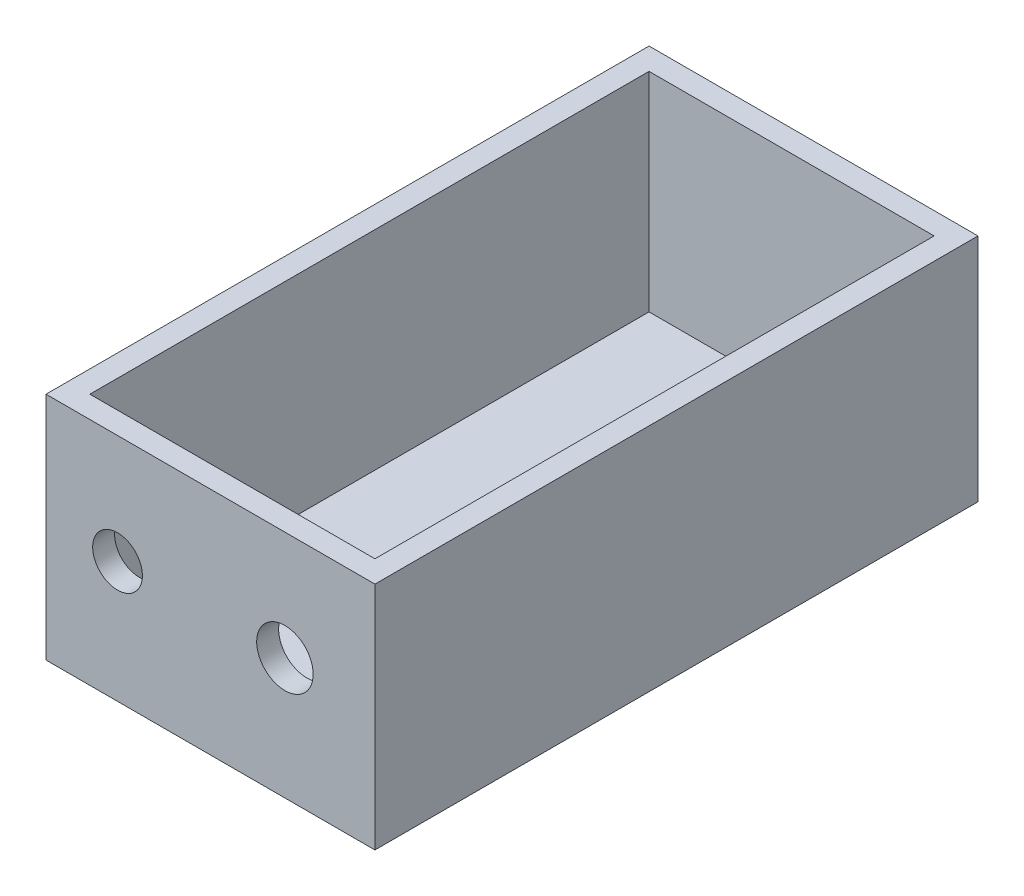
SolidWorks part; units mm, degrees
ref_plane "Спереди" through (0, 0, 0) normal (0, 0, 1) x (1, 0, 0)
ref_plane "Сверху" through (0, 0, 0) normal (0, 1, 0) x (1, 0, 0)
ref_plane "Справа" through (0, 0, 0) normal (1, 0, 0) x (0, 0, -1)
sketch "Эскиз1" plane through (0, 0, 0) normal (0, 1, 0) x (1, 0, 0)
  line L1 (0, 0) -> (30, 0)
  line L2 (0, 0) -> (0, 55)
  line L3 (0, 55) -> (30, 55)
  line L4 (30, 0) -> (30, 55)
  dimension "D1" = 30
  dimension "D2" = 55
extrude "Бобышка-Вытянуть1" add sketch "Эскиз1" along normal blind 21
sketch "Эскиз2" plane through (0, 21, 0) normal (0, 1, 0) x (1, 0, 0)
  line L8 (2, 2) -> (28, 2)
  line L9 (28, 2) -> (28, 53)
  line L10 (28, 53) -> (2, 53)
  line L11 (2, 53) -> (2, 2)
  line L12 (2, 2) -> (28, 2)
  line L13 (28, 2) -> (28, 53)
  line L14 (28, 53) -> (2, 53)
  line L15 (2, 53) -> (2, 2)
  dimension "D1" = 2
extrude "Вырез-Вытянуть1" cut sketch "Эскиз2" against normal blind 19
sketch "Эскиз3" plane through (0, 0, 0) normal (0, 0, 1) x (1, 0, 0)
  circle A0 centre (6.5241, 11.0547) radius 2.2671
  circle A1 centre (21.7896, 11.0547) radius 2.5738
extrude "Вырез-Вытянуть2" cut sketch "Эскиз3" against normal blind 3
